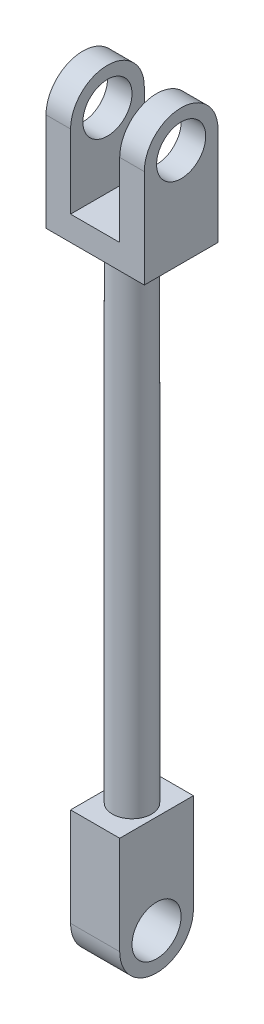
SolidWorks part; units mm, degrees
material "Brass"
ref_plane "Front Plane" through (0, 0, 0) normal (0, 0, 1) x (1, 0, 0)
ref_plane "Top Plane" through (0, 0, 0) normal (0, 1, 0) x (1, 0, 0)
ref_plane "Right Plane" through (0, 0, 0) normal (1, 0, 0) x (0, 0, -1)
sketch "Sketch1" plane through (0, 0, 0) normal (0, 1, 0) x (1, 0, 0)
  circle A0 centre (0, 0) radius 4
  dimension "D1" = 8
extrude "Boss-Extrude1" add sketch "Sketch1" along normal mid plane 100
sketch "Sketch2" plane through (0, 0, 0) normal (1, 0, 0) x (0, 0, -1)
  line L0 (0, 50) -> (7.5, 50)
  line L1 (4, 50) -> (-4, 50) construction
  line L2 (7.5, 50) -> (7.5, 70)
  line L3 (0, 50) -> (-7.5, 50)
  line L4 (-7.5, 50) -> (-7.5, 70)
  arc A0 (-7.5, 70) -> (7.5, 70) centre (0, 70) cw
  dimension "D1" = 7.5
  dimension "D2" = 20
extrude "Boss-Extrude2" add sketch "Sketch2" along normal mid plane 20
sketch "Sketch3" plane through (10, 0, 0) normal (1, 0, 0) x (0, 0, -1)
  line L0 (0, 11) -> (0, -11) construction
  circle A0 centre (0, 70) radius 5
  arc A1 (7.5, 70) -> (-7.5, 70) centre (0, 70) ccw construction
  dimension "D1" = 10
extrude "Cut-Extrude1" cut sketch "Sketch3" against normal through all
sketch "Sketch4" plane through (0, 0, 7.5) normal (0, 0, 1) x (1, 0, 0)
  line L0 (10, 77.5) -> (-10, 77.5) construction
  line L1 (-5, 55) -> (5, 55)
  line L2 (-5, 55) -> (-5, 77.5)
  line L3 (-5, 77.5) -> (5, 77.5)
  line L4 (5, 55) -> (5, 77.5)
  line L5 (10, 70) -> (10, 50) construction
  line L6 (10, 50) -> (-10, 50) construction
  dimension "D1" = 10
  dimension "D2" = 5
  dimension "D3" = 5
extrude "Cut-Extrude2" cut sketch "Sketch4" against normal through all
sketch "Sketch5" plane through (0, 0, 0) normal (1, 0, 0) x (0, 0, -1)
  line L0 (-4, -50) -> (4, -50) construction
  line L1 (-7.5, -50) -> (7.5, -50)
  line L2 (-7.5, -50) -> (-7.5, -70)
  line L3 (0, 11) -> (0, -11) construction
  line L4 (7.5, -50) -> (7.5, -70)
  arc A0 (-7.5, -70) -> (7.5, -70) centre (0, -70) ccw
  dimension "D4" = 7.5
  dimension "D1" = 15
  dimension "D2" = 7.5
  dimension "D3" = 20
extrude "Boss-Extrude3" add sketch "Sketch5" along normal mid plane 10
sketch "Sketch6" plane through (5, 0, 0) normal (1, 0, 0) x (0, 0, -1)
  circle A0 centre (0, -70) radius 5
  arc A1 (-7.5, -70) -> (7.5, -70) centre (0, -70) ccw construction
  dimension "D1" = 10
extrude "Cut-Extrude3" cut sketch "Sketch6" against normal blind 20
